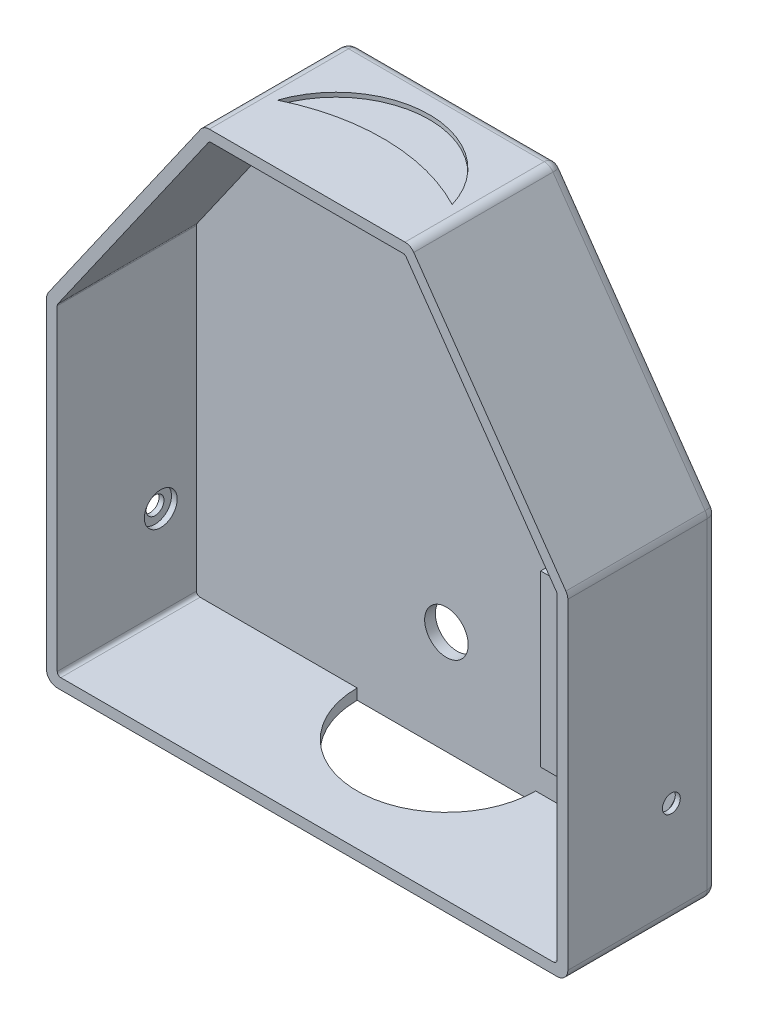
SolidWorks part; units mm, degrees
material "PS HI"
ref_plane "Face" through (0, 0, 0) normal (0, 0, 1) x (1, 0, 0)
ref_plane "Dessus" through (0, 0, 0) normal (0, 1, 0) x (1, 0, 0)
ref_plane "Droite" through (0, 0, 0) normal (1, 0, 0) x (0, 0, -1)
sketch "Esquisse1" plane through (0, 0, 0) normal (0, 0, 1) x (1, 0, 0)
  line L0 (0, 150.8391) -> (0, -183.5075) construction
  line L1 (70, 0) -> (-70, 0)
  line L2 (-70, 0) -> (-70, 90)
  line L3 (-70, 90) -> (-27.4, 150.8391)
  line L4 (-27.4, 150.8391) -> (27.4, 150.8391)
  line L5 (70, 0) -> (70, 90)
  line L6 (70, 90) -> (27.4, 150.8391)
  line L7 (-73, 90.9459) -> (-28.9617, 153.8391)
  line L8 (-28.9617, 153.8391) -> (28.9617, 153.8391)
  line L9 (73, 90.9459) -> (28.9617, 153.8391)
  line L10 (73, -3) -> (73, 90.9459)
  line L11 (73, -3) -> (-73, -3)
  line L12 (-73, -3) -> (-73, 90.9459)
  line L13 (-70, 90) -> (-27.4, 150.8391)
  line L14 (27.4, 150.8391) -> (70, 90)
  point P8 (0, 0)
  dimension "D1" = 70
  dimension "D2" = 90
  dimension "D3" = 35
  dimension "D4" = 27.4
  dimension "D5" = 3
extrude "Boss.-Extru.2" add sketch "Esquisse1" along normal blind 42 contours L1 L2 L3 L4 L6 L5 | L7 L8 L9 L10 L11 L12
sketch "Esquisse3" plane through (0, 0, 0) normal (0, 0, 1) x (1, 0, 0)
  line L0 (-70, 90) -> (-27.4, 150.8391)
  line L1 (-27.4, 150.8391) -> (27.4, 150.8391)
  line L2 (27.4, 150.8391) -> (70, 90)
  line L3 (70, 90) -> (70, 0)
  line L4 (70, 0) -> (-70, 0)
  line L5 (-70, 0) -> (-70, 90)
extrude "Boss.-Extru.3" add sketch "Esquisse3" along normal blind 3
fillet "Congé5" radius 1 6 edges at (-27.4, 150.8391, 22.5) (-70, 90, 22.5) (-70, 0, 22.5) (70, 0, 22.5) (27.4, 150.8391, 22.5) (70, 90, 22.5)
fillet "Congé6" radius 3 6 edges at (28.9617, 153.8391, 21) (73, 90.9459, 21) (73, -3, 21) (-73, -3, 21) (-73, 90.9459, 21) (-28.9617, 153.8391, 21)
fillet "Congé7" radius 3 12 edges at (72.1213, -2.1213, 0) (73, 45, 0) (72.8612, 90.9021, 0) (51.1575, 122.1403, 0) (28.7852, 153.5001, 0) (0, 153.8391, 0) (-28.7852, 153.5001, 0) (-51.1575, 122.1403, 0) (-72.8612, 90.9021, 0) (-73, 45, 0) (-72.1213, -2.1213, 0) (0, -3, 0)
sketch "Esquisse4" plane through (-70, 0, 0) normal (1, 0, 0) x (0, 0, -1)
  line L0 (-42, 1) -> (-3, 1) construction
  line L1 (-3, 89.6847) -> (-3, 1) construction
  circle A0 centre (-13, 26) radius 4.6
  point P4 (-22.5, 1)
  point P8 (-13, 26)
  dimension "D1" = 9.2
  dimension "D2" = 25
  dimension "D3" = 10
extrude "Enlèv. mat.-Extru.1" cut sketch "Esquisse4" against normal blind 1.6
sketch "Esquisse5" plane through (-70, 0, 0) normal (1, 0, 0) x (0, 0, -1)
  circle A0 centre (-13, 26) radius 2.5
  point P4 (-13, 26)
  dimension "D1" = 5
extrude "Enlèv. mat.-Extru.2" cut sketch "Esquisse5" against normal through all
sketch "Esquisse6" plane through (70, 0, 0) normal (-1, 0, 0) x (0, 0, 1)
  line L0 (3, 1) -> (3, 89.6847) construction
  line L1 (3, 1) -> (42, 1) construction
  circle A0 centre (13, 26) radius 4.6
  point P7 (13, 26)
  dimension "D1" = 9.2
  dimension "D2" = 10
  dimension "D3" = 25
extrude "Enlèv. mat.-Extru.3" cut sketch "Esquisse6" against normal blind 1.6
sketch "Esquisse7" plane through (70, 0, 0) normal (-1, 0, 0) x (0, 0, 1)
  circle A0 centre (13, 26) radius 2.5
  dimension "D1" = 5
extrude "Enlèv. mat.-Extru.4" cut sketch "Esquisse7" against normal through all
sketch "Esquisse12" plane through (0, 153.8391, 0) normal (0, 1, 0) x (1, 0, 0)
  line L0 (-27.4, -3) -> (-27.4, -42) construction
  line L1 (27.4, -42) -> (27.4, -3) construction
  arc A0 (24.9, -26.2914) -> (-24.9, -25.4245) centre (-0.1381, -33.7921) ccw
  arc A1 (24.9, -26.2914) -> (-24.9, -25.4245) centre (-0.8569, -75.0862) ccw
  dimension "D3" = 26.1375
  dimension "D1" = 2.5
  dimension "D2" = 2.5
extrude "Enlèv. mat.-Extru.8" cut sketch "Esquisse12" against normal blind 1.2
sketch "Esquisse13" plane through (70, 0, 0) normal (-1, 0, 0) x (0, 0, 1)
  line L0 (3, 88.6847) -> (37.6, 88.6847)
  line L1 (3, 1) -> (3, 89.6847) construction
  line L2 (37.6, 88.6847) -> (37.6, 43.0847)
  line L3 (37.6, 43.0847) -> (3, 43.0847)
  line L4 (3, 89.6847) -> (38.6, 89.6847)
  line L5 (38.6, 89.6847) -> (38.6, 42.0847)
  line L6 (38.6, 42.0847) -> (3, 42.0847)
  line L7 (42, 89.6847) -> (3, 89.6847) construction
  line L8 (3, 89.6847) -> (3, 42.0847)
  line M2 (3, 89.6847) -> (3, 1)
  line M5 (42, 89.6847) -> (3, 89.6847)
  dimension "D1" = 45.6
  dimension "D2" = 34.6
  dimension "D3" = 1
extrude "Boss.-Extru.4" add sketch "Esquisse13" along normal blind 8 contours L6 L5 L0 L2 L3 M5 M2
sketch "Esquisse14" plane through (0, 0, 3) normal (0, 0, 1) x (1, 0, 0)
  line L0 (0, 0) -> (0, 171.7553) construction
  line L1 (-69, 0) -> (69, 0) construction
  line L2 (-78.8746, 26) -> (101.1798, 26) construction
  circle A0 centre (0, 26) radius 6.1
  point P6 (0, 26)
  dimension "D2" = 12.2
  dimension "D1" = 26
extrude "Enlèv. mat.-Extru.9" cut sketch "Esquisse14" against normal through all
sketch "Esquisse16" plane through (0, -3, 0) normal (0, -1, 0) x (1, 0, 0)
  line L0 (-70, 3) -> (70, 3) construction
  line L1 (0, -21.8674) -> (0, 93.0784) construction
  line L2 (-25, 3) -> (25, 3)
  arc A0 (-25, 3) -> (25, 3) centre (0, 3) cw
  dimension "D1" = 25
  dimension "D2" = 45
extrude "Enlèv. mat.-Extru.11" cut sketch "Esquisse16" against normal up to surface (3 mm away) up to face at (0, 0, 22.5)
